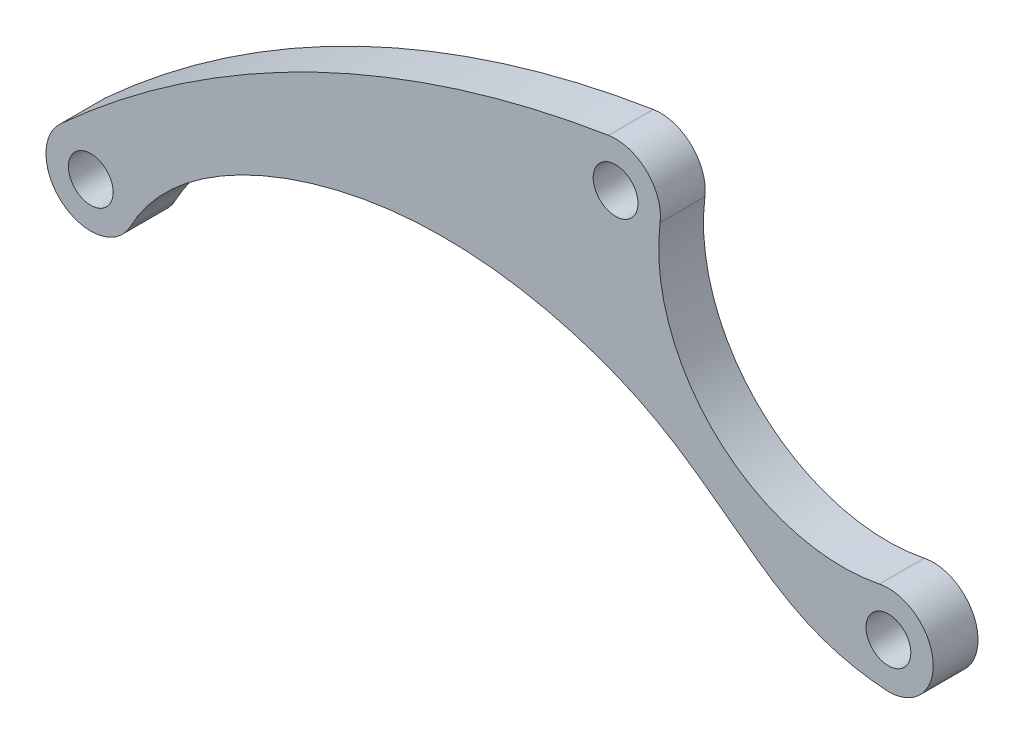
SolidWorks part; units mm, degrees
ref_plane "前基準面" through (0, 0, 0) normal (0, 0, 1) x (1, 0, 0)
ref_plane "上基準面" through (0, 0, 0) normal (0, 1, 0) x (1, 0, 0)
ref_plane "右基準面" through (0, 0, 0) normal (1, 0, 0) x (0, 0, -1)
sketch "草圖1" plane through (0, 0, 0) normal (0, 0, 1) x (1, 0, 0)
  line L0 (0, 0) -> (89, 0) construction
  line L1 (89, 0) -> (58.5604, 28.2078) construction
  line L2 (58.5604, 28.2078) -> (0, 0) construction
  line L4 (0, -5) -> (89, -5)
  line L5 (92.3985, 3.6674) -> (61.9589, 31.8752)
  circle A0 centre (89, 0) radius 2.5
  circle A1 centre (58.5604, 28.2078) radius 2.5
  circle A2 centre (0, 0) radius 2.5
  arc A3 (61.9589, 31.8752) -> (58.28, 33.1999) centre (58.5604, 28.2078) ccw
  arc A4 (-3.7288, 3.3311) -> (0, -5) centre (0, 0) ccw
  arc A5 (89, -5) -> (92.3985, 3.6674) centre (89, 0) ccw
  circle A6 centre (58.5604, 28.2078) radius 5 construction
  circle A7 centre (89, 0) radius 5 construction
  circle A8 centre (0, 0) radius 5 construction
  arc A9 (-3.7288, 3.3311) -> (58.28, 33.1999) centre (63.3221, -56.5683) cw
  dimension "D4" = 5
  dimension "D1" = 89
  dimension "D2" = 41.5
  dimension "D3" = 65
  dimension "D5" = 2.5
extrude "填料-伸長1" add sketch "草圖1" along normal mid plane 5
sketch "草圖2" plane through (0, 0, 2.5) normal (0, 0, 1) x (1, 0, 0)
  arc A0 (89, -5) -> (92.3985, 3.6674) centre (89, 0) ccw construction
  arc A1 (-3.7288, 3.3311) -> (0, -5) centre (0, 0) ccw construction
  arc A2 (61.9589, 31.8752) -> (58.28, 33.1999) centre (58.5604, 28.2078) ccw construction
  arc A3 (89, -5) -> (88.0024, 4.8995) centre (89, 0) ccw
  arc A4 (-3.3693, 3.6943) -> (4.4261, -2.3258) centre (0, 0) ccw
  arc A5 (63.5215, 27.5854) -> (57.7719, 33.1452) centre (58.5604, 28.2078) ccw
  arc A6 (57.7719, 33.1452) -> (-3.3693, 3.6943) centre (76.4533, -83.8291) ccw
  arc A7 (63.5215, 27.5854) -> (88.0024, 4.8995) centre (83.9037, 25.0284) ccw
  spline S0 degree 3 poles (4.4261, -2.3258) (8.3328, 5.1086) (26.8007, 15.2151) (48.7403, 14.4731) (64.3474, 8.1954) (74.8177, -0.2316) (81.7848, -4.538) (89, -5) knots 0 0 0 0 0.281769 0.583331 0.690815 0.820319 1 1 1 1
extrude "除料-伸長1" cut sketch "草圖2" against normal blind 5 flip side to cut
